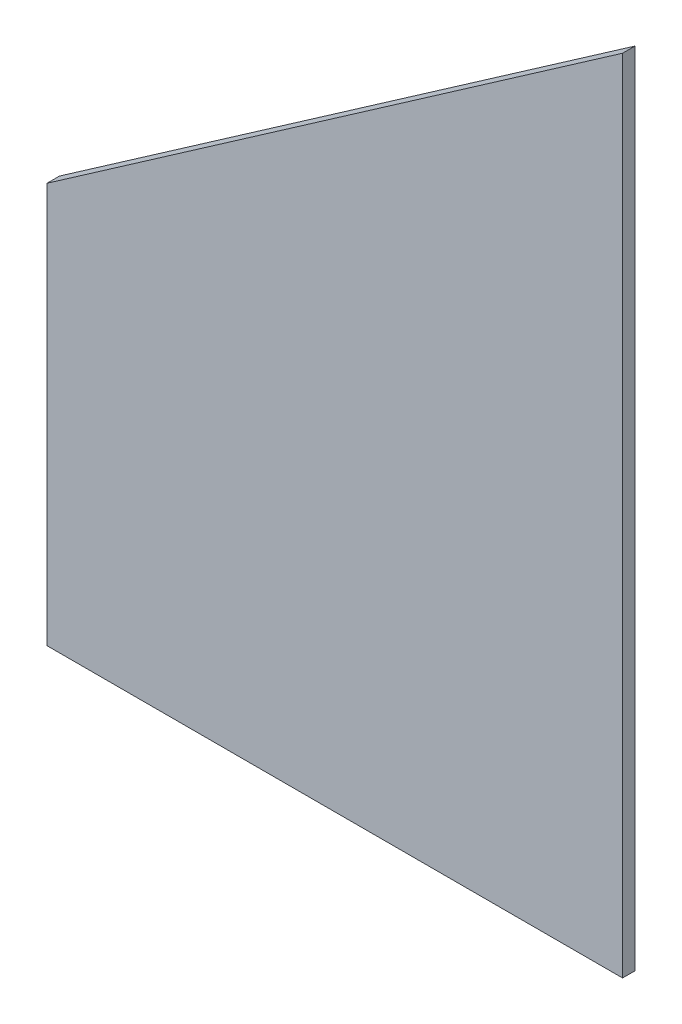
SolidWorks part; units mm, degrees
material "A-Glass Fiber"
ref_plane "Front Plane" through (0, 0, 0) normal (0, 0, 1) x (1, 0, 0)
ref_plane "Top Plane" through (0, 0, 0) normal (0, 1, 0) x (1, 0, 0)
ref_plane "Right Plane" through (0, 0, 0) normal (1, 0, 0) x (0, 0, -1)
sketch "Sketch1" plane through (0, 0, 0) normal (0, 0, 1) x (1, 0, 0)
  line L3 (-184.15, -8.89) -> (-38.1, -8.89)
  line L4 (-38.1, -8.89) -> (-38.1, 0)
  line L6 (-184.15, -8.89) -> (-184.15, 92.71)
  line L7 (-184.15, 92.71) -> (-38.1, 194.31)
  line L8 (-38.1, 194.31) -> (-38.1, 0)
  dimension "D1" = 203.2
  dimension "D2" = 146.05
  dimension "D6" = 101.6
extrude "Boss-Extrude1" add sketch "Sketch1" along normal blind 3.175
